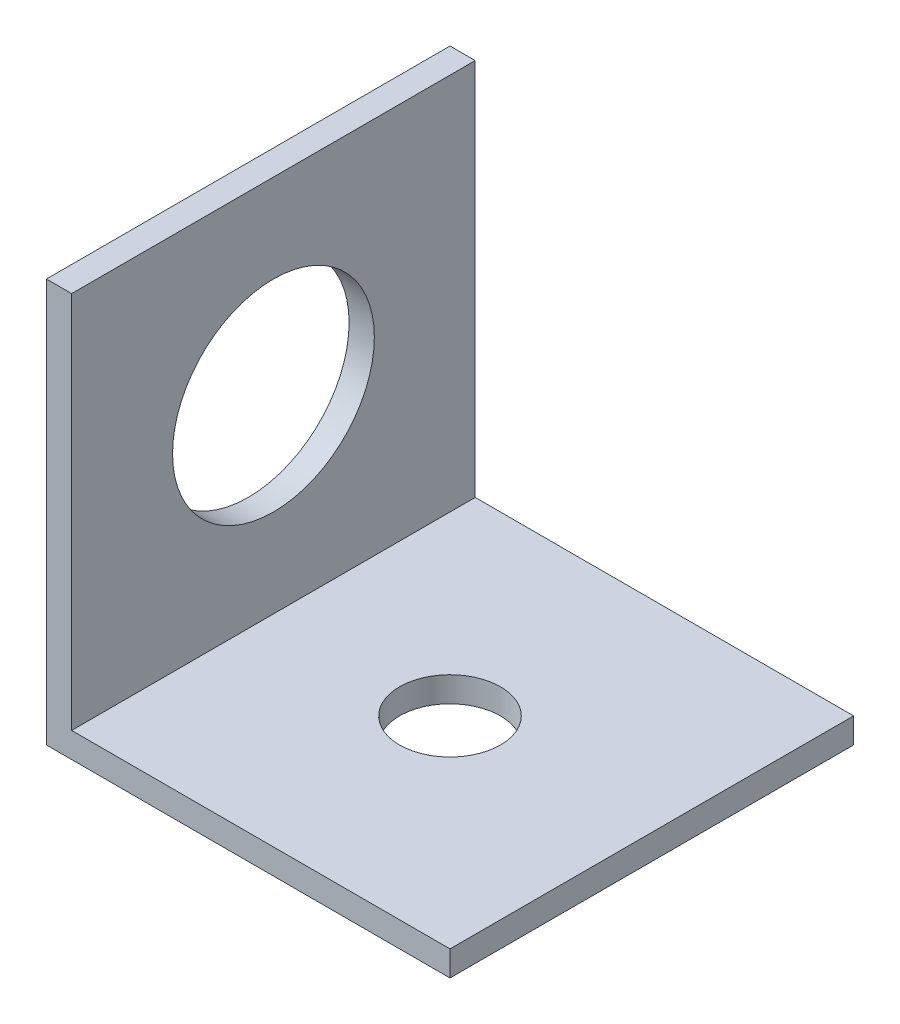
SolidWorks part; units mm, degrees
ref_plane "Front Plane" through (0, 0, 0) normal (0, 0, 1) x (1, 0, 0)
ref_plane "Top Plane" through (0, 0, 0) normal (0, 1, 0) x (1, 0, 0)
ref_plane "Right Plane" through (0, 0, 0) normal (1, 0, 0) x (0, 0, -1)
sketch "Sketch1" plane through (0, 0, 0) normal (0, 0, 1) x (1, 0, 0)
  line L0 (0, 0) -> (0, 25.4)
  line L1 (0, 25.4) -> (1.5875, 25.4)
  line L2 (1.5875, 25.4) -> (1.5875, 1.5875)
  line L3 (1.5875, 1.5875) -> (25.4, 1.5875)
  line L4 (25.4, 1.5875) -> (25.4, 0)
  line L5 (25.4, 0) -> (0, 0)
  dimension "D1" = 25.4
  dimension "D2" = 25.4
  dimension "D3" = 1.5875
  dimension "D4" = 1.5875
  dimension "D5" = 23.8125
extrude "Boss-Extrude1" add sketch "Sketch1" along normal blind 25.4
sketch "Sketch2" plane through (0, 1.5875, 0) normal (0, 1, 0) x (1, 0, 0)
  line L0 (0, -25.4) -> (25.4, 0) construction
  line L1 (0, -25.4) -> (0, 0) construction
  circle A0 centre (12.7, -12.7) radius 3.175
  point P7 (0, 0)
  dimension "D1" = 6.35
extrude "Cut-Extrude1" cut sketch "Sketch2" against normal blind 25.4
sketch "Sketch3" plane through (1.5875, 0, 0) normal (1, 0, 0) x (0, 0, -1)
  line L0 (-25.4, 1.5875) -> (0, 25.4) construction
  circle A0 centre (-12.7, 13.4938) radius 6.35
  dimension "D1" = 12.7
extrude "Cut-Extrude2" cut sketch "Sketch3" against normal blind 25.4
